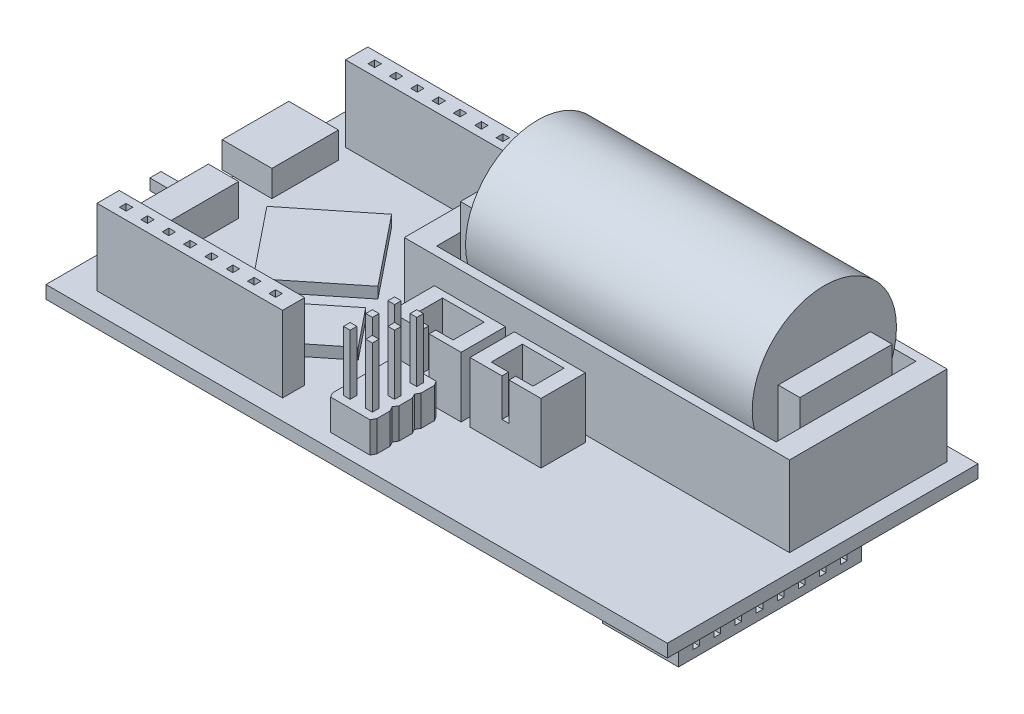
SolidWorks part; units mm, degrees
ref_plane "Front Plane" through (0, 0, 0) normal (0, 0, 1) x (1, 0, 0)
ref_plane "Top Plane" through (0, 0, 0) normal (0, 1, 0) x (1, 0, 0)
ref_plane "Right Plane" through (0, 0, 0) normal (1, 0, 0) x (0, 0, -1)
sketch "Sketch1" plane through (0, 0, 0) normal (0, 1, 0) x (1, 0, 0)
  line L1 (-35, -17.5) -> (35, -17.5)
  line L2 (-35, -17.5) -> (-35, 17.5)
  line L3 (-35, 17.5) -> (35, 17.5)
  line L4 (35, -17.5) -> (35, 17.5)
  point P0 (0, 0)
  dimension "D1" = 70
  dimension "D2" = 35
extrude "Boss-Extrude1" add sketch "Sketch1" along normal blind 1.45
sketch "Sketch2" plane through (0, 1.45, 0) normal (0, 1, 0) x (1, 0, 0)
  line L0 (-35, 17.5) -> (-35, -17.5) construction
  line L1 (-34, -0.2) -> (-30.6, -0.2)
  line L2 (-34, -0.2) -> (-34, -12)
  line L3 (-34, -12) -> (-30.6, -12)
  line L4 (-30.6, -0.2) -> (-30.6, -12)
  line L5 (-35, -17.5) -> (35, -17.5) construction
  dimension "D1" = 3.4
  dimension "D2" = 11.8
  dimension "D3" = 1
  dimension "D4" = 5.5
extrude "Boss-Extrude2" add sketch "Sketch2" along normal blind 3.6
sketch "Sketch3" plane through (0, 1.45, 0) normal (0, 1, 0) x (1, 0, 0)
  line L0 (-35, 17.5) -> (-35, -17.5) construction
  line L1 (-36.25, 11.1) -> (-30.65, 11.1)
  line L2 (-36.25, 11.1) -> (-36.25, 3.6)
  line L3 (-36.25, 3.6) -> (-30.65, 3.6)
  line L4 (-30.65, 11.1) -> (-30.65, 3.6)
  line L5 (35, 17.5) -> (-35, 17.5) construction
  dimension "D1" = 1.25
  dimension "D2" = 7.5
  dimension "D3" = 5.6
  dimension "D4" = 6.4
extrude "Boss-Extrude3" add sketch "Sketch3" along normal blind 2.95
sketch "Sketch4" plane through (-34, 0, 0) normal (-1, 0, 0) x (0, 0, 1)
  line L0 (0.2, 5.05) -> (0.2, 1.45) construction
  line L1 (3.35, 4.8) -> (8.85, 4.8)
  line L2 (3.35, 4.8) -> (3.35, 3.55)
  line L3 (3.35, 3.55) -> (8.85, 3.55)
  line L4 (8.85, 4.8) -> (8.85, 3.55)
  line L7 (0.2, 5.05) -> (12, 5.05) construction
  dimension "D1" = 5.5
  dimension "D2" = 3.15
  dimension "D3" = 0.25
  dimension "D4" = 1.25
extrude "Cut-Extrude1" cut sketch "Sketch4" against normal blind 2
sketch "Sketch5" plane through (-32, 0, 0) normal (-1, 0, 0) x (0, 0, 1)
  line L0 (3.35, 3.55) -> (8.85, 3.55) construction
  line L1 (3.35, 4.8) -> (4.6, 4.8)
  line L2 (3.35, 4.8) -> (3.35, 3.55)
  line L3 (3.35, 3.55) -> (4.6, 3.55)
  line L4 (4.6, 4.8) -> (4.6, 3.55)
  dimension "D1" = 1.25
extrude "Boss-Extrude4" add sketch "Sketch5" along normal blind 4.2
sketch "Sketch7" plane through (-36.25, 0, 0) normal (-1, 0, 0) x (0, 0, 1)
  spline S0 degree 1 poles (-3.6, 4.4) (-11.1, 4.4) knots 0 0 1 1
sketch "Sketch11" plane through (0, 1.45, 0) normal (0, 1, 0) x (1, 0, 0)
  line L0 (35, 17.5) -> (-35, 17.5) construction
  line L1 (-31.5, 15.25) -> (-10.6, 15.25)
  line L2 (-31.5, 15.25) -> (-31.5, 12.75)
  line L3 (-31.5, 12.75) -> (-10.6, 12.75)
  line L4 (-10.6, 15.25) -> (-10.6, 12.75)
  line L5 (-31.5, -12.75) -> (-10.6, -12.75)
  line L6 (-31.5, -12.75) -> (-31.5, -15.25)
  line L7 (-31.5, -15.25) -> (-10.6, -15.25)
  line L8 (-10.6, -12.75) -> (-10.6, -15.25)
  line L9 (-35, -17.5) -> (35, -17.5) construction
  line L10 (-35, 17.5) -> (-35, 11.1) construction
  dimension "D1" = 20.9
  dimension "D2" = 2.5
  dimension "D3" = 2.25
  dimension "D4" = 2.25
  dimension "D5" = 3.5
extrude "Boss-Extrude5" add sketch "Sketch11" along normal blind 8.55
sketch "Sketch12" plane through (0, 1.45, 0) normal (0, 1, 0) x (1, 0, 0)
  line L0 (-28.9348, 1.3149) -> (-21.1355, 7.5736)
  line L1 (-21.1355, 7.5736) -> (-14.8768, -0.2257)
  line L2 (-14.8768, -0.2257) -> (-22.6761, -6.4844)
  line L3 (-22.6761, -6.4844) -> (-28.9348, 1.3149)
  dimension "D1" = 10
  dimension "D2" = 10
extrude "Boss-Extrude6" add sketch "Sketch12" along normal blind 1.25
sketch "Sketch13" plane through (0, 1.45, 0) normal (0, 1, 0) x (1, 0, 0)
  line L0 (-19.1293, -7.5448) -> (-13.4748, -3.0073)
  line L1 (-22.6761, -6.4844) -> (-14.8768, -0.2257) construction
  line L2 (-13.4748, -3.0073) -> (-10.0325, -7.2969)
  line L3 (-10.0325, -7.2969) -> (-15.687, -11.8344)
  line L4 (-15.687, -11.8344) -> (-19.1293, -7.5448)
  dimension "D1" = 7.25
  dimension "D2" = 5.5
extrude "Boss-Extrude7" add sketch "Sketch13" along normal blind 1.25
sketch "Sketch14" plane through (0, 1.45, 0) normal (0, 1, 0) x (1, 0, 0)
  line L0 (-10.6, 12.75) -> (-10.6, 15.25) construction
  line L1 (-10.35, 15.9646) -> (33.05, 15.9646)
  line L2 (-10.35, 15.9646) -> (-10.35, -1.7854)
  line L3 (-10.35, -1.7854) -> (33.05, -1.7854)
  line L4 (33.05, 15.9646) -> (33.05, -1.7854)
  point P6 (-10.6, 14)
  dimension "D1" = 43.4
  dimension "D2" = 17.75
  dimension "D3" = 0.25
extrude "Boss-Extrude8" add sketch "Sketch14" along normal blind 9.05
sketch "Sketch15" plane through (0, 10.5, 0) normal (0, 1, 0) x (1, 0, 0)
  line L0 (33.05, 15.9646) -> (-10.35, 15.9646) construction
  line L1 (-7.7, 14.9646) -> (30.55, 14.9646)
  line L2 (-7.7, 14.9646) -> (-7.7, -0.7854)
  line L3 (-7.7, -0.7854) -> (30.55, -0.7854)
  line L4 (30.55, 14.9646) -> (30.55, -0.7854)
  line L5 (-10.35, -1.7854) -> (33.05, -1.7854) construction
  line L6 (33.05, -1.7854) -> (33.05, 15.9646) construction
  line L7 (-10.35, 15.9646) -> (-10.35, -1.7854) construction
  dimension "D1" = 1
  dimension "D2" = 1
  dimension "D3" = 2.5
  dimension "D4" = 2.65
extrude "Cut-Extrude3" cut sketch "Sketch15" against normal blind 9.05 contours L2 L1 L4 L3
sketch "Sketch16" plane through (-7.7, 0, 0) normal (1, 0, 0) x (0, 0, -1)
  line L0 (14.9646, 1.45) -> (-0.7854, 1.45) construction
  line L1 (1.8896, 1.45) -> (12.2896, 1.45)
  line L2 (1.8896, 1.45) -> (1.8896, 13.5)
  line L3 (1.8896, 13.5) -> (12.2896, 13.5)
  line L4 (12.2896, 1.45) -> (12.2896, 13.5)
  line L6 (14.9646, 1.45) -> (14.9646, 10.5) construction
  dimension "D1" = 10.4
  dimension "D2" = 2.675
  dimension "D3" = 12.05
extrude "Boss-Extrude9" add sketch "Sketch16" along normal blind 3.5
sketch "Sketch17" plane through (30.55, 0, 0) normal (-1, 0, 0) x (0, 0, 1)
  line L0 (-14.9646, 1.45) -> (0.7854, 1.45) construction
  line L1 (-12.2846, 1.45) -> (-1.8846, 1.45)
  line L2 (-12.2846, 1.45) -> (-12.2846, 13.5)
  line L3 (-12.2846, 13.5) -> (-1.8846, 13.5)
  line L4 (-1.8846, 1.45) -> (-1.8846, 13.5)
  line L5 (-14.9646, 1.45) -> (-14.9646, 10.5) construction
  dimension "D1" = 10.4
  dimension "D2" = 2.68
  dimension "D3" = 12.05
extrude "Boss-Extrude10" add sketch "Sketch17" along normal blind 2.6
sketch "Sketch18" plane through (-4.2, 0, 0) normal (1, 0, 0) x (0, 0, -1)
  line L0 (12.2896, 1.45) -> (12.2896, 13.5) construction
  circle A0 centre (7.0896, 12.4748) radius 8.125
  dimension "D1" = 16.25
  dimension "D2" = 5.2
extrude "Boss-Extrude11" add sketch "Sketch18" along normal blind 32.3
sketch "Sketch19" plane through (0, 1.45, 0) normal (0, 1, 0) x (1, 0, 0)
  line L0 (2.8, -2.5354) -> (10.8, -2.5354)
  line L1 (-6.2, -2.5354) -> (1.8, -2.5354)
  line L2 (-6.2, -2.5354) -> (-6.2, -7.5354)
  line L3 (-6.2, -7.5354) -> (1.8, -7.5354)
  line L4 (1.8, -2.5354) -> (1.8, -7.5354)
  line L5 (2.8, -2.5354) -> (2.8, -7.5354)
  line L6 (2.8, -7.5354) -> (10.8, -7.5354)
  line L7 (10.8, -2.5354) -> (10.8, -7.5354)
  line L8 (-10.35, -1.7854) -> (33.05, -1.7854) construction
  line L10 (-10.6, -15.25) -> (-10.6, -12.75) construction
  dimension "D1" = 8
  dimension "D2" = 5
  dimension "D3" = 8
  dimension "D4" = 5
  dimension "D5" = 1
  dimension "D6" = 0.75
  dimension "D7" = 4.4
extrude "Boss-Extrude12" add sketch "Sketch19" along normal blind 6.8
sketch "Sketch20" plane through (0, 8.25, 0) normal (0, 1, 0) x (1, 0, 0)
  line L0 (-6.2, -7.5354) -> (1.8, -7.5354) construction
  line L1 (-4.55, -3.2854) -> (0.15, -3.2854)
  line L2 (-4.55, -3.2854) -> (-4.55, -6.7854)
  line L3 (-4.55, -6.7854) -> (0.15, -6.7854)
  line L4 (0.15, -3.2854) -> (0.15, -6.7854)
  line L5 (4.45, -3.2854) -> (9.15, -3.2854)
  line L6 (4.45, -3.2854) -> (4.45, -6.7854)
  line L7 (4.45, -6.7854) -> (9.15, -6.7854)
  line L8 (1.8, -7.5354) -> (1.8, -2.5354) construction
  line L9 (9.15, -3.2854) -> (9.15, -6.7854)
  line L10 (10.8, -7.5354) -> (10.8, -2.5354) construction
  line L11 (2.8, -7.5354) -> (10.8, -7.5354) construction
  dimension "D1" = 4.7
  dimension "D2" = 3.5
  dimension "D3" = 0.75
  dimension "D4" = 1.65
  dimension "D5" = 4.7
  dimension "D6" = 3.5
  dimension "D7" = 1.65
  dimension "D8" = 0.75
extrude "Cut-Extrude4" cut sketch "Sketch20" against normal blind 6.8
sketch "Sketch21" plane through (0, 8.25, 0) normal (0, 1, 0) x (1, 0, 0)
  line L0 (-4.55, -6.7854) -> (0.15, -6.7854) construction
  line L1 (-2.6, -6.7854) -> (-1.8, -6.7854)
  line L2 (-2.6, -6.7854) -> (-2.6, -7.5354)
  line L3 (-2.6, -7.5354) -> (-1.8, -7.5354)
  line L4 (-1.8, -6.7854) -> (-1.8, -7.5354)
  line L5 (-6.2, -7.5354) -> (1.8, -7.5354) construction
  line L6 (4.45, -6.7854) -> (9.15, -6.7854) construction
  line L7 (6.4, -6.7854) -> (7.2, -6.7854)
  line L8 (6.4, -6.7854) -> (6.4, -7.5354)
  line L9 (6.4, -7.5354) -> (7.2, -7.5354)
  line L10 (7.2, -6.7854) -> (7.2, -7.5354)
  line L11 (2.8, -7.5354) -> (10.8, -7.5354) construction
  line L13 (0.15, -6.7854) -> (0.15, -3.2854) construction
  line L15 (9.15, -6.7854) -> (9.15, -3.2854) construction
  dimension "D1" = 0.8
  dimension "D2" = 1.95
  dimension "D3" = 1.95
  dimension "D4" = 0.8
extrude "Cut-Extrude5" cut sketch "Sketch21" against normal blind 4.25
sketch "Sketch23" plane through (0, 1.45, 0) normal (0, 1, 0) x (1, 0, 0)
  line L0 (-35, -17.5) -> (35, -17.5) construction
  line L1 (-3.8328, -8.4) -> (-0.8328, -8.4)
  line L2 (-3.8328, -8.4) -> (-3.8328, -15.9)
  line L3 (-3.8328, -15.9) -> (-0.8328, -15.9)
  line L4 (-0.8328, -8.4) -> (-0.8328, -15.9)
  dimension "D1" = 3
  dimension "D2" = 7.5
  dimension "D3" = 1.6
extrude "Boss-Extrude13" add sketch "Sketch23" along normal blind 3.45
sketch "Sketch26" plane through (0, 1.45, 0) normal (0, 1, 0) x (1, 0, 0)
  line L0 (-0.8328, -8.4) -> (-0.1455, -8.4)
  line L1 (-3.8328, -8.4) -> (-3.8328, -15.9) construction
  line L2 (-0.8328, -15.9) -> (-0.8328, -8.4) construction
  line L4 (-0.1455, -8.4) -> (0.1672, -8.9)
  line L6 (-3.8328, -8.4) -> (-3.8328, -10.9)
  line L7 (-4.5296, -10.9) -> (-4.8328, -10.4)
  line L8 (-4.8328, -10.4) -> (-4.8328, -8.9)
  line L11 (-4.5296, -10.9) -> (-3.8328, -10.9)
  line L12 (-3.8328, -8.4) -> (-4.5296, -8.4)
  line L13 (-4.5296, -8.4) -> (-4.8328, -8.9)
  line L14 (0.1672, -8.9) -> (0.1672, -10.4)
  line L15 (0.1672, -10.4) -> (-0.1005, -10.9)
  line L16 (-0.1005, -10.9) -> (-0.8328, -10.9)
  line L17 (-0.8328, -10.9) -> (-0.8328, -8.4)
  dimension "D1" = 1.5
  dimension "D3" = 1.5
  dimension "D4" = 1
  dimension "D5" = 0.5
  dimension "D6" = 1
  dimension "D7" = 0.5
extrude "Boss-Extrude17" add sketch "Sketch26" along normal blind 3.45
sketch "Sketch27" plane through (0, 1.45, 0) normal (0, 1, 0) x (1, 0, 0)
  line L0 (-3.8328, -10.9) -> (-4.5296, -10.9)
  line L1 (-4.5296, -10.9) -> (-4.8328, -11.4)
  line L2 (-4.8328, -11.4) -> (-4.8328, -12.9)
  line L3 (-4.8328, -12.9) -> (-4.5296, -13.4)
  line L4 (-4.5296, -13.4) -> (-3.8328, -13.4)
  line L5 (-3.8328, -10.9) -> (-3.8328, -15.9) construction
  line L6 (-3.8328, -13.4) -> (-3.8328, -10.9)
  line L7 (-0.8328, -10.9) -> (-0.1005, -10.9)
  line L8 (-0.1005, -10.9) -> (0.1672, -11.4)
  line L9 (0.1672, -11.4) -> (0.1672, -12.9)
  line L10 (0.1672, -12.9) -> (-0.1269, -13.3849)
  line L11 (-0.1269, -13.3849) -> (-0.8328, -13.3849)
  line L12 (-0.8328, -15.9) -> (-0.8328, -10.9) construction
  line L13 (-0.8328, -13.3849) -> (-0.8328, -10.9)
  dimension "D1" = 1.5
  dimension "D2" = 1.5
  dimension "D3" = 1
  dimension "D4" = 0.5
  dimension "D5" = 0.5
  dimension "D6" = 1
extrude "Boss-Extrude18" add sketch "Sketch27" along normal blind 3.45
sketch "Sketch28" plane through (0, 1.45, 0) normal (0, 1, 0) x (1, 0, 0)
  line L0 (-3.8328, -13.4) -> (-4.5296, -13.4)
  line L1 (-4.5296, -13.4) -> (-4.8328, -13.9)
  line L2 (-4.8328, -13.9) -> (-4.8328, -15.4)
  line L3 (-4.8328, -15.4) -> (-4.5296, -15.9)
  line L4 (-4.5296, -15.9) -> (-3.8328, -15.9)
  line L5 (-0.8328, -13.3849) -> (-0.1269, -13.3849)
  line L6 (-0.1269, -13.3849) -> (0.1672, -13.8849)
  line L7 (0.1672, -13.8849) -> (0.1672, -15.3849)
  line L8 (0.1672, -15.3849) -> (-0.0996, -15.9)
  line L9 (-0.0996, -15.9) -> (-0.8328, -15.9)
  line L10 (-0.8328, -15.9) -> (-0.8328, -13.3849)
  line L12 (-3.8328, -13.4) -> (-3.8328, -15.9)
  dimension "D1" = 1.5
  dimension "D2" = 1.5
  dimension "D3" = 0.5
  dimension "D4" = 1
  dimension "D5" = 0.5
  dimension "D6" = 1
extrude "Boss-Extrude19" add sketch "Sketch28" along normal blind 3.45
sketch "Sketch32" plane through (0, 0, 0) normal (0, -1, 0) x (1, 0, 0)
  line L0 (-35, 17.5) -> (35, 17.5) construction
  line L1 (25.45, 15.25) -> (34, 15.25)
  line L2 (25.45, 15.25) -> (25.45, -5.4)
  line L3 (25.45, -5.4) -> (34, -5.4)
  line L4 (34, 15.25) -> (34, -5.4)
  line L5 (35, 17.5) -> (35, -17.5) construction
  dimension "D1" = 20.65
  dimension "D2" = 8.55
  dimension "D3" = 2.25
  dimension "D4" = 1
extrude "Boss-Extrude23" add sketch "Sketch32" along normal blind 2.5
sketch "Sketch33" plane through (0, 0, 0) normal (0, -1, 0) x (1, 0, 0)
  line L0 (-35, 17.5) -> (35, 17.5) construction
  line L1 (1.6, 15.9) -> (15, 15.9)
  line L2 (1.6, 15.9) -> (1.6, -3.1)
  line L3 (1.6, -3.1) -> (15, -3.1)
  line L4 (15, 15.9) -> (15, -3.1)
  line L5 (35, 17.5) -> (35, -17.5) construction
  dimension "D1" = 19
  dimension "D2" = 13.4
  dimension "D3" = 1.6
  dimension "D4" = 20
extrude "Boss-Extrude24" add sketch "Sketch33" along normal blind 0.875
sketch "Sketch34" plane through (0, -0.875, 0) normal (0, -1, 0) x (1, 0, 0)
  line L0 (1.6, -3.1) -> (15, -3.1) construction
  line L1 (5.05, 3.5) -> (10.25, 3.5)
  line L2 (5.05, 3.5) -> (5.05, -1.7)
  line L3 (5.05, -1.7) -> (10.25, -1.7)
  line L4 (10.25, 3.5) -> (10.25, -1.7)
  line L5 (15, -3.1) -> (15, 15.9) construction
  line L6 (1.6, 15.9) -> (1.6, -3.1) construction
  dimension "D1" = 1.4
  dimension "D2" = 4.75
  dimension "D3" = 3.45
extrude "Boss-Extrude25" add sketch "Sketch34" along normal blind 0.875
sketch "Sketch35" plane through (0, 10, 0) normal (0, 1, 0) x (1, 0, 0)
  line L0 (-31.5, 12.75) -> (-10.6, 12.75) construction
  line L1 (-29.845, 14.375) -> (-29.095, 14.375)
  line L2 (-29.845, 14.375) -> (-29.845, 13.625)
  line L3 (-29.845, 13.625) -> (-29.095, 13.625)
  line L4 (-29.095, 14.375) -> (-29.095, 13.625)
  line L6 (-31.5, 15.25) -> (-31.5, 12.75) construction
  line L8 (-27.44, 14.375) -> (-26.69, 14.375)
  line L9 (-27.44, 14.375) -> (-27.44, 13.625)
  line L10 (-27.44, 13.625) -> (-26.69, 13.625)
  line L11 (-26.69, 14.375) -> (-26.69, 13.625)
  line L12 (-25.035, 14.375) -> (-24.285, 14.375)
  line L13 (-25.035, 14.375) -> (-25.035, 13.625)
  line L14 (-25.035, 13.625) -> (-24.285, 13.625)
  line L15 (-24.285, 14.375) -> (-24.285, 13.625)
  line L16 (-22.63, 14.375) -> (-21.88, 14.375)
  line L17 (-22.63, 14.375) -> (-22.63, 13.625)
  line L18 (-22.63, 13.625) -> (-21.88, 13.625)
  line L19 (-21.88, 14.375) -> (-21.88, 13.625)
  line L20 (-20.225, 14.375) -> (-19.475, 14.375)
  line L21 (-20.225, 14.375) -> (-20.225, 13.625)
  line L22 (-20.225, 13.625) -> (-19.475, 13.625)
  line L23 (-19.475, 14.375) -> (-19.475, 13.625)
  line L24 (-17.82, 14.375) -> (-17.07, 14.375)
  line L25 (-17.82, 14.375) -> (-17.82, 13.625)
  line L26 (-17.82, 13.625) -> (-17.07, 13.625)
  line L27 (-17.07, 14.375) -> (-17.07, 13.625)
  line L28 (-15.415, 14.375) -> (-14.665, 14.375)
  line L29 (-15.415, 14.375) -> (-15.415, 13.625)
  line L30 (-15.415, 13.625) -> (-14.665, 13.625)
  line L31 (-14.665, 14.375) -> (-14.665, 13.625)
  line L32 (-13.01, 14.375) -> (-12.26, 14.375)
  line L33 (-13.01, 14.375) -> (-13.01, 13.625)
  line L34 (-13.01, 13.625) -> (-12.26, 13.625)
  line L35 (-12.26, 14.375) -> (-12.26, 13.625)
  dimension "D1" = 0.75
  dimension "D2" = 0.75
  dimension "D3" = 0.875
  dimension "D4" = 1.655
  dimension "D5" = 1.655
  dimension "D6" = 1.655
  dimension "D7" = 1.655
  dimension "D8" = 1.655
  dimension "D9" = 1.655
  dimension "D10" = 1.655
  dimension "D11" = 1.655
extrude "Cut-Extrude6" cut sketch "Sketch35" against normal blind 6.75
sketch "Sketch36" plane through (0, 10, 0) normal (0, 1, 0) x (1, 0, 0)
  line L0 (-10.6, -12.75) -> (-31.5, -12.75) construction
  line L1 (-29.845, -13.625) -> (-29.095, -13.625)
  line L2 (-29.845, -13.625) -> (-29.845, -14.375)
  line L3 (-29.845, -14.375) -> (-29.095, -14.375)
  line L4 (-29.095, -13.625) -> (-29.095, -14.375)
  line L6 (-31.5, -12.75) -> (-31.5, -15.25) construction
  line L8 (-27.44, -13.625) -> (-26.69, -13.625)
  line L9 (-27.44, -13.625) -> (-27.44, -14.375)
  line L10 (-27.44, -14.375) -> (-26.69, -14.375)
  line L11 (-26.69, -13.625) -> (-26.69, -14.375)
  line L12 (-25.035, -13.625) -> (-24.285, -13.625)
  line L13 (-25.035, -13.625) -> (-25.035, -14.375)
  line L14 (-25.035, -14.375) -> (-24.285, -14.375)
  line L15 (-24.285, -13.625) -> (-24.285, -14.375)
  line L16 (-22.63, -13.625) -> (-21.88, -13.625)
  line L17 (-22.63, -13.625) -> (-22.63, -14.375)
  line L18 (-22.63, -14.375) -> (-21.88, -14.375)
  line L19 (-21.88, -13.625) -> (-21.88, -14.375)
  line L20 (-20.225, -13.625) -> (-19.475, -13.625)
  line L21 (-20.225, -13.625) -> (-20.225, -14.375)
  line L22 (-20.225, -14.375) -> (-19.475, -14.375)
  line L23 (-19.475, -13.625) -> (-19.475, -14.375)
  line L24 (-17.82, -13.625) -> (-17.07, -13.625)
  line L25 (-17.82, -13.625) -> (-17.82, -14.375)
  line L26 (-17.82, -14.375) -> (-17.07, -14.375)
  line L27 (-17.07, -13.625) -> (-17.07, -14.375)
  line L28 (-15.415, -13.625) -> (-14.665, -13.625)
  line L29 (-15.415, -13.625) -> (-15.415, -14.375)
  line L30 (-15.415, -14.375) -> (-14.665, -14.375)
  line L31 (-14.665, -13.625) -> (-14.665, -14.375)
  line L32 (-13.01, -13.625) -> (-12.26, -13.625)
  line L33 (-13.01, -13.625) -> (-13.01, -14.375)
  line L34 (-13.01, -14.375) -> (-12.26, -14.375)
  line L35 (-12.26, -13.625) -> (-12.26, -14.375)
  point P36 (-29.095, -14)
  dimension "D1" = 0.75
  dimension "D2" = 0.75
  dimension "D3" = 0.875
  dimension "D4" = 1.655
  dimension "D5" = 1.655
  dimension "D6" = 1.655
  dimension "D7" = 1.655
  dimension "D8" = 1.655
  dimension "D9" = 1.655
  dimension "D10" = 1.655
  dimension "D11" = 1.655
extrude "Cut-Extrude7" cut sketch "Sketch36" against normal blind 6.75
sketch "Sketch37" plane through (34, 0, 0) normal (1, 0, 0) x (0, 0, -1)
  line L0 (5.4, -2.5) -> (-15.25, -2.5) construction
  line L1 (-13.623, -0.875) -> (-12.873, -0.875)
  line L2 (-13.623, -0.875) -> (-13.623, -1.625)
  line L3 (-13.623, -1.625) -> (-12.873, -1.625)
  line L4 (-12.873, -0.875) -> (-12.873, -1.625)
  line L6 (-15.25, -2.5) -> (-15.25, 0) construction
  line L8 (-11.246, -0.875) -> (-10.496, -0.875)
  line L9 (-11.246, -0.875) -> (-11.246, -1.625)
  line L10 (-11.246, -1.625) -> (-10.496, -1.625)
  line L11 (-10.496, -0.875) -> (-10.496, -1.625)
  line L12 (-8.869, -0.875) -> (-8.119, -0.875)
  line L13 (-8.869, -0.875) -> (-8.869, -1.625)
  line L14 (-8.869, -1.625) -> (-8.119, -1.625)
  line L15 (-8.119, -0.875) -> (-8.119, -1.625)
  line L16 (-6.492, -0.875) -> (-5.742, -0.875)
  line L17 (-6.492, -0.875) -> (-6.492, -1.625)
  line L18 (-6.492, -1.625) -> (-5.742, -1.625)
  line L19 (-5.742, -0.875) -> (-5.742, -1.625)
  line L20 (-4.115, -0.875) -> (-3.365, -0.875)
  line L21 (-4.115, -0.875) -> (-4.115, -1.625)
  line L22 (-4.115, -1.625) -> (-3.365, -1.625)
  line L23 (-3.365, -0.875) -> (-3.365, -1.625)
  line L24 (-1.738, -0.875) -> (-0.988, -0.875)
  line L25 (-1.738, -0.875) -> (-1.738, -1.625)
  line L26 (-1.738, -1.625) -> (-0.988, -1.625)
  line L27 (-0.988, -0.875) -> (-0.988, -1.625)
  line L28 (0.639, -0.875) -> (1.389, -0.875)
  line L29 (0.639, -0.875) -> (0.639, -1.625)
  line L30 (0.639, -1.625) -> (1.389, -1.625)
  line L31 (1.389, -0.875) -> (1.389, -1.625)
  line L32 (3.016, -0.875) -> (3.766, -0.875)
  line L33 (3.016, -0.875) -> (3.016, -1.625)
  line L34 (3.016, -1.625) -> (3.766, -1.625)
  line L35 (3.766, -0.875) -> (3.766, -1.625)
  dimension "D1" = 0.75
  dimension "D2" = 0.75
  dimension "D3" = 0.875
  dimension "D4" = 1.627
  dimension "D5" = 1.627
  dimension "D6" = 1.627
  dimension "D7" = 1.627
  dimension "D8" = 1.627
  dimension "D9" = 1.627
  dimension "D10" = 1.627
  dimension "D11" = 1.627
extrude "Cut-Extrude8" cut sketch "Sketch37" against normal blind 6.75
sketch "Sketch38" plane through (-36.25, 0, 0) normal (-1, 0, 0) x (0, 0, 1)
  line L1 (-10.6561, 4.0023) -> (-4.0425, 4.0023)
  line L2 (-10.6561, 4.0023) -> (-10.6561, 1.8473)
  line L3 (-10.6561, 1.8473) -> (-4.0425, 1.8473)
  line L4 (-4.0425, 4.0023) -> (-4.0425, 1.8473)
extrude "Cut-Extrude9" cut sketch "Sketch38" against normal blind 5
sketch "Sketch39" plane through (0, 4.9, 0) normal (0, 1, 0) x (1, 0, 0)
  line L0 (-4.8328, -8.9) -> (-4.8328, -10.4) construction
  line L1 (-3.9578, -9.275) -> (-3.2078, -9.275)
  line L2 (-3.9578, -9.275) -> (-3.9578, -10.025)
  line L3 (-3.9578, -10.025) -> (-3.2078, -10.025)
  line L4 (-3.2078, -9.275) -> (-3.2078, -10.025)
  line L5 (-0.1455, -8.4) -> (-4.5296, -8.4) construction
  line L6 (-1.4578, -9.275) -> (-0.7078, -9.275)
  line L7 (-1.4578, -9.275) -> (-1.4578, -10.025)
  line L8 (-1.4578, -10.025) -> (-0.7078, -10.025)
  line L9 (-0.7078, -9.275) -> (-0.7078, -10.025)
  line L10 (-3.9578, -11.775) -> (-3.2078, -11.775)
  line L11 (-3.9578, -11.775) -> (-3.9578, -12.525)
  line L12 (-3.9578, -12.525) -> (-3.2078, -12.525)
  line L13 (-3.2078, -11.775) -> (-3.2078, -12.525)
  line L14 (-3.9578, -14.275) -> (-3.2078, -14.275)
  line L15 (-3.9578, -14.275) -> (-3.9578, -15.025)
  line L16 (-3.9578, -15.025) -> (-3.2078, -15.025)
  line L17 (-3.2078, -14.275) -> (-3.2078, -15.025)
  line L18 (0.1672, -10.4) -> (0.1672, -8.9) construction
  line L19 (-1.4578, -11.775) -> (-0.7078, -11.775)
  line L20 (-1.4578, -11.775) -> (-1.4578, -12.525)
  line L21 (-1.4578, -12.525) -> (-0.7078, -12.525)
  line L22 (-0.7078, -11.775) -> (-0.7078, -12.525)
  line L23 (-1.4578, -14.275) -> (-0.7078, -14.275)
  line L24 (-1.4578, -14.275) -> (-1.4578, -15.025)
  line L25 (-1.4578, -15.025) -> (-0.7078, -15.025)
  line L26 (-0.7078, -14.275) -> (-0.7078, -15.025)
  line L27 (-4.5296, -15.9) -> (-0.0996, -15.9) construction
  dimension "D1" = 0.75
  dimension "D2" = 0.375
  dimension "D3" = 0.875
  dimension "D4" = 0.375
  dimension "D5" = 0.375
  dimension "D6" = 0.875
extrude "Boss-Extrude26" add sketch "Sketch39" along normal blind 6.75
